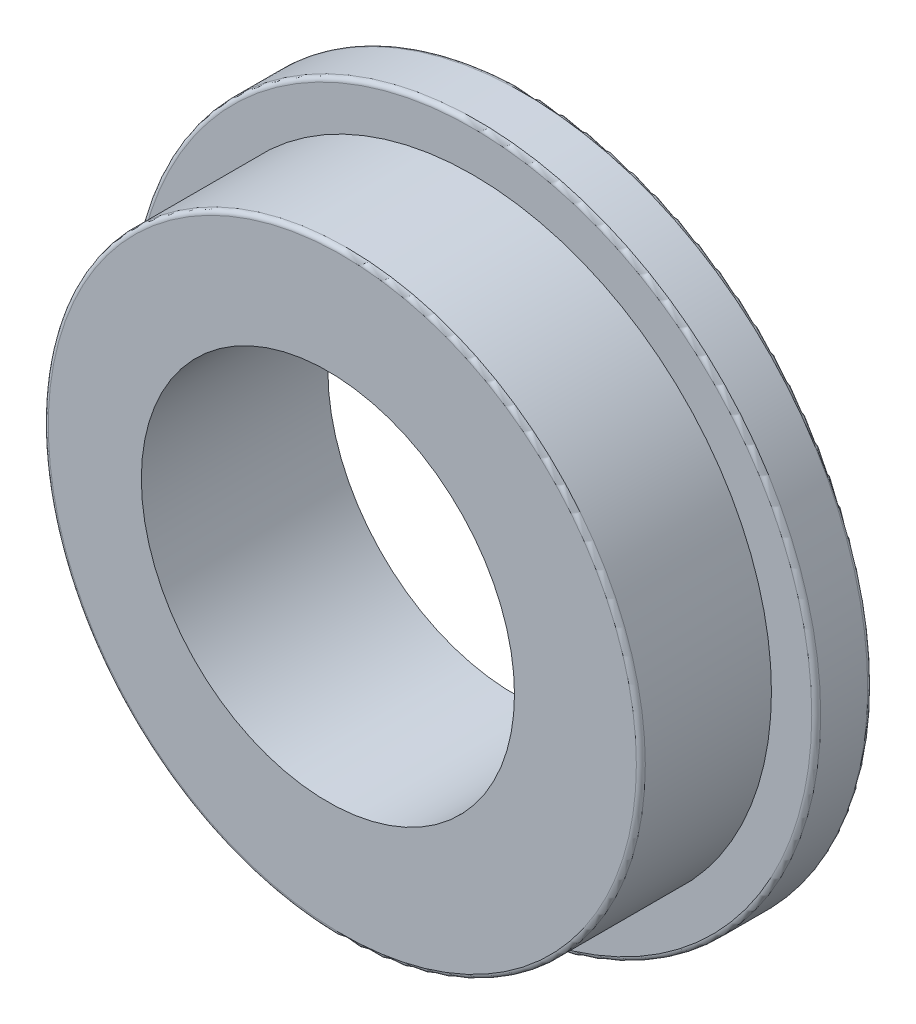
SolidWorks part; units mm, degrees
ref_plane "Front Plane" through (0, 0, 0) normal (0, 0, 1) x (1, 0, 0)
ref_plane "Top Plane" through (0, 0, 0) normal (0, 1, 0) x (1, 0, 0)
ref_plane "Right Plane" through (0, 0, 0) normal (1, 0, 0) x (0, 0, -1)
sketch "Sketch1" plane through (0, 0, 0) normal (0, 0, 1) x (1, 0, 0)
  circle A0 centre (0, 0) radius 4.6
  dimension "D1" = 9.2
extrude "Boss-Extrude1" add sketch "Sketch1" along normal blind 0.75 contours A0
sketch "Sketch2" plane through (0, 0, 0.75) normal (0, 0, 1) x (1, 0, 0)
  circle A0 centre (0, 0) radius 4
  dimension "D1" = 8
extrude "Boss-Extrude2" add sketch "Sketch2" along normal blind 1.75
sketch "Sketch3" plane through (0, 0, 2.5) normal (0, 0, 1) x (1, 0, 0)
  circle A1 centre (-0.1931, 0) radius 2.5
  dimension "D1" = 5
extrude "Cut-Extrude1" cut sketch "Sketch3" against normal through all
fillet "Fillet1" radius 0.06 3 edges at (4.6, 0, 0) (4.6, 0, 0.75) (4, 0, 2.5)
